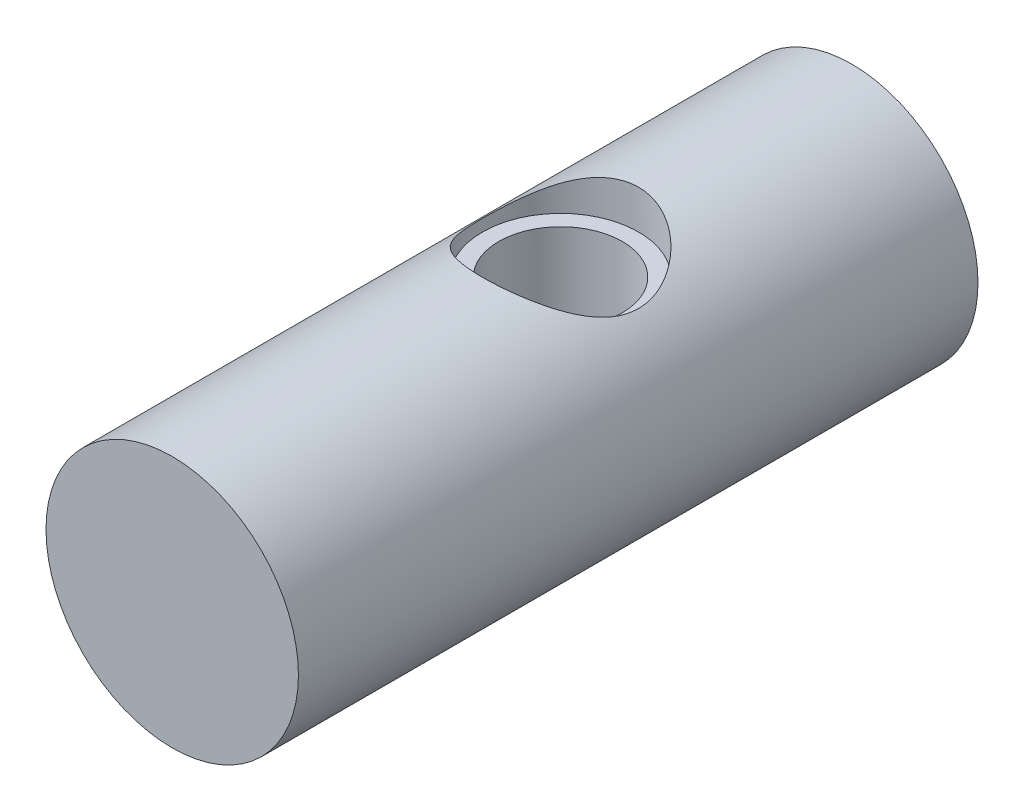
SolidWorks part; units mm, degrees
material "6061-T6 (SS)"
ref_plane "Front Plane" through (0, 0, 0) normal (0, 0, 1) x (1, 0, 0)
ref_plane "Top Plane" through (0, 0, 0) normal (0, 1, 0) x (1, 0, 0)
ref_plane "Right Plane" through (0, 0, 0) normal (1, 0, 0) x (0, 0, -1)
sketch "Sketch1" plane through (0, 0, 0) normal (0, 0, 1) x (1, 0, 0)
  circle A0 centre (0, 0) radius 4.1275
  dimension "D1" = 8.255
extrude "Boss-Extrude1" add sketch "Sketch1" along normal blind 22.225
ref_plane "Plane1" through (0, 0, 9.525) normal (0, 0, 1) x (1, 0, 0)
hole_wizard "#7 (0.201) Diameter Hole1" positions "3DSketch2" profile "Sketch7" hole size "#7" standard "ANSI Inch"
sketch3d "3DSketch2"
  point P0 (0, 4.1275, 9.525)
sketch "Sketch7" plane through (0, 4.1275, 9.525) normal (1, 0, 0) x (0, 0, 1)
  line L0 (0, 0) -> (0, 1.27)
  line L1 (0, 1.27) -> (2.5527, 1.27)
  line L2 (2.5527, 1.27) -> (2.5527, 0)
  line L5 (2.5527, 0) -> (0, 0)
  line L10 (0, 1.27) -> (-2.5527, 1.27) construction
  line L11 (0, -6.35) -> (0, 107.95) construction
  dimension "Hole Dia." = 5.1054
  dimension "Hole Depth" = 1.27
  dimension "Drill Angle" = 180
hole_wizard "#10-32 Tapped Hole1" positions "3DSketch1" profile "Sketch6" tap size "#10-32" standard "ANSI Inch" end condition through all
sketch3d "3DSketch1"
  point P0 (0, 4.1275, 9.525)
sketch "Sketch6" plane through (0, 4.1275, 9.525) normal (1, 0, 0) x (0, 0, 1)
  line L0 (0, 0) -> (0, 8.255)
  line L1 (0, 8.255) -> (2.0193, 8.255)
  line L2 (2.0193, 8.255) -> (2.0193, 0)
  line L5 (2.0193, 0) -> (0, 0)
  line L11 (0, -6.35) -> (0, 107.95) construction
  dimension "Thru Tap Drill Dia." = 4.0386
  dimension "Thru Tap Drill Depth" = 8.255
cosmetic thread "Hole Thread2"
